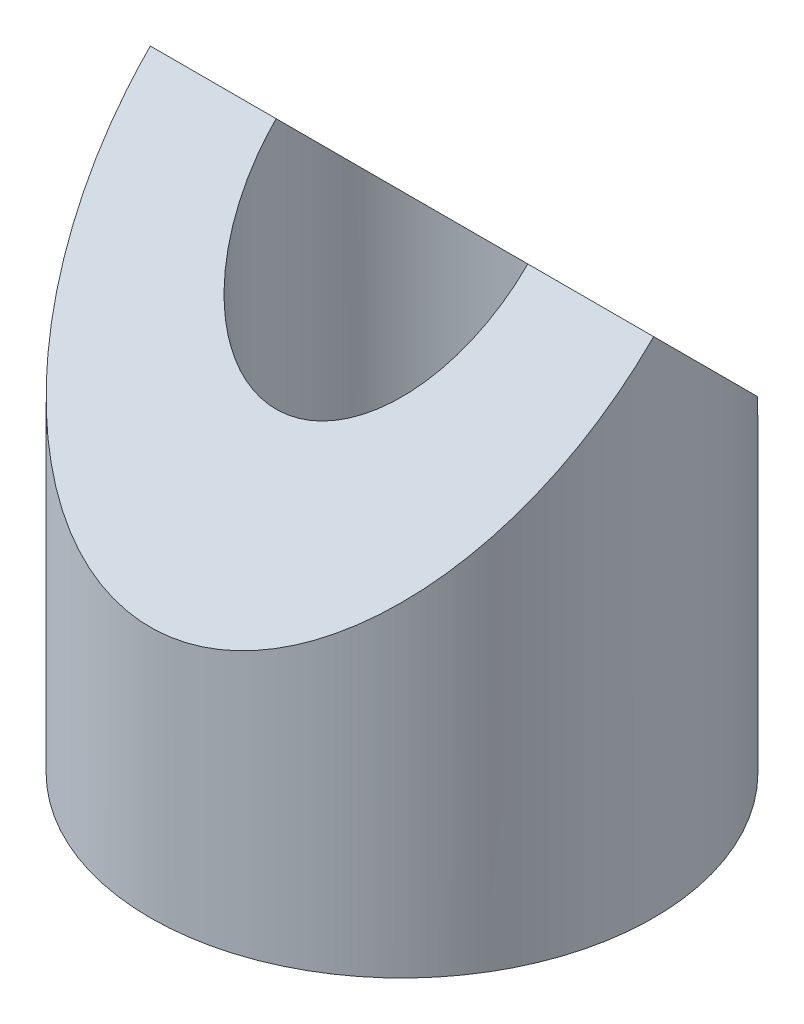
SolidWorks part; units mm, degrees
ref_plane "Front" through (0, 0, 0) normal (0, 0, 1) x (1, 0, 0)
ref_plane "Top" through (0, 0, 0) normal (0, 1, 0) x (1, 0, 0)
ref_plane "Right" through (0, 0, 0) normal (1, 0, 0) x (0, 0, -1)
sketch "Sketch1" plane through (0, 0, 0) normal (0, 1, 0) x (1, 0, 0)
  circle A0 centre (0, 0) radius 2
  circle A1 centre (0, 0) radius 1
  dimension "D1" = 4
  dimension "D2" = 2
extrude "Boss-Extrude1" add sketch "Sketch1" along normal blind 4
sketch "Sketch2" plane through (0, 0, 0) normal (1, 0, 0) x (0, 0, -1)
  line L0 (-2, 2) -> (0, 4)
  line L1 (-2, 4) -> (-2, 0) construction
  line L2 (2, 4) -> (-2, 4) construction
  line L3 (0, 4) -> (2, 2)
  line L4 (2, 0) -> (2, 4) construction
  line L5 (2, 2) -> (2, 4)
  line L6 (2, 4) -> (-2, 4)
  line L7 (-2, 4) -> (-2, 2)
extrude "Cut-Extrude1" cut sketch "Sketch2" against normal mid plane 4 contours L5 L6 L3 | L6 L7 L0
